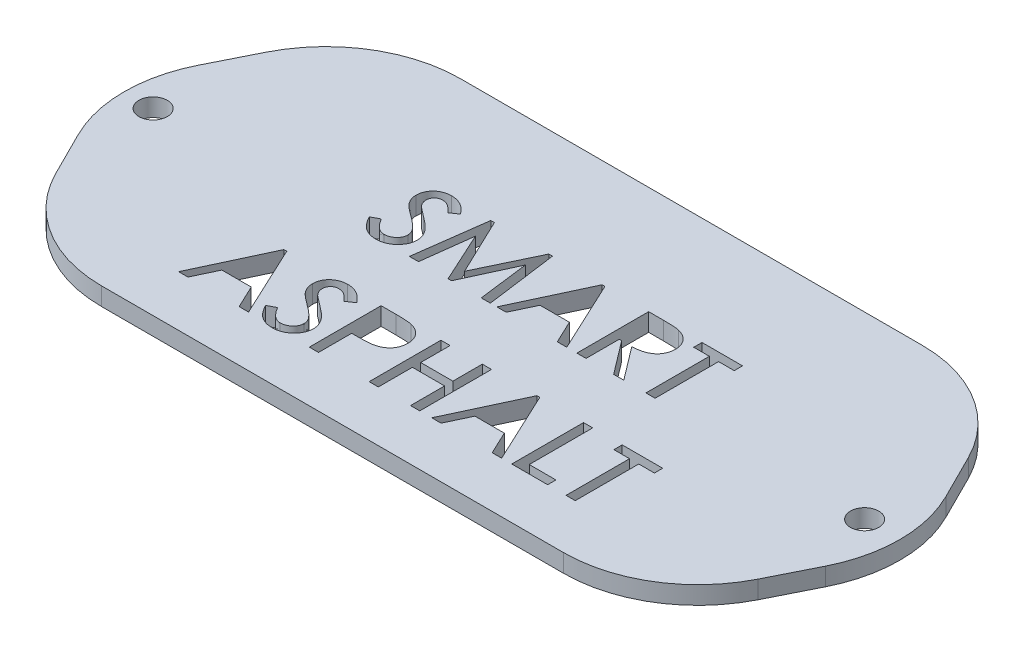
SolidWorks part; units mm, degrees
ref_plane "Front Plane" through (0, 0, 0) normal (0, 0, 1) x (1, 0, 0)
ref_plane "Top Plane" through (0, 0, 0) normal (0, 1, 0) x (1, 0, 0)
ref_plane "Right Plane" through (0, 0, 0) normal (1, 0, 0) x (0, 0, -1)
sketch "Sketch1" plane through (0, 0, 0) normal (0, 1, 0) x (1, 0, 0)
  line L0 (-31.8082, -3.672) -> (38.1918, -3.672) construction
  line L1 (-22.5377, 16.328) -> (28.9212, 16.328)
  line L2 (-31.8082, 16.328) -> (-31.8082, -23.672)
  line L3 (-22.5377, -23.672) -> (28.9212, -23.672)
  line L4 (38.1918, 16.328) -> (38.1918, -23.672)
  line L5 (-35.9541, -15.3802) -> (-38.4541, -10.3802)
  line L6 (-38.4541, 3.0362) -> (-35.9541, 8.0362)
  line L7 (42.3377, 8.0362) -> (44.8377, 3.0362)
  line L8 (44.8377, -10.3802) -> (42.3377, -15.3802)
  line L9 (-31.8082, -3.672) -> (-41.8082, -3.672) construction
  line L10 (48.1918, -3.672) -> (38.1918, -3.672) construction
  line L11 (-14.2954, -2.0854) -> (-13.4236, -1.6207)
  line L12 (-9.4749, 3.2607) -> (-10.3114, 2.687)
  line L13 (-8.2441, -3.672) -> (-7.1752, 4.328)
  line L14 (-7.1752, 4.328) -> (-6.7714, 4.328)
  line L15 (-6.7714, 4.328) -> (-3.7377, -2.0309)
  line L16 (-3.7377, -2.0309) -> (-0.7041, 4.328)
  line L17 (-0.7041, 4.328) -> (-0.2938, 4.328)
  line L18 (-0.2938, 4.328) -> (0.7815, -3.672)
  line L19 (0.7815, -3.672) -> (-0.2361, -3.672)
  line L20 (-0.2361, -3.672) -> (-0.9477, 1.9691)
  line L21 (-0.9477, 1.9691) -> (-3.5438, -3.672)
  line L22 (-3.5438, -3.672) -> (-3.9316, -3.672)
  line L23 (-3.9316, -3.672) -> (-6.5198, 1.9691)
  line L24 (-6.5198, 1.9691) -> (-7.2281, -3.672)
  line L25 (-7.2281, -3.672) -> (-8.2441, -3.672)
  line L26 (5.5507, 4.328) -> (9.2943, -3.672)
  line L27 (9.2943, -3.672) -> (8.2414, -3.672)
  line L28 (8.2414, -3.672) -> (7.0267, -1.1079)
  line L29 (7.0267, -1.1079) -> (3.7543, -1.1079)
  line L30 (3.7543, -1.1079) -> (2.5395, -3.672)
  line L31 (2.5395, -3.672) -> (1.4994, -3.672)
  line L32 (1.4994, -3.672) -> (5.2302, 4.328)
  line L33 (5.2302, 4.328) -> (5.5507, 4.328)
  line L34 (5.3905, 2.5796) -> (4.1453, -0.1848)
  line L35 (4.1453, -0.1848) -> (6.6485, -0.1848)
  line L36 (6.6485, -0.1848) -> (5.3905, 2.5796)
  line L37 (10.4225, 4.328) -> (12.0603, 4.328)
  line L38 (12.852, 0.0204) -> (15.6533, -3.672)
  line L39 (15.6533, -3.672) -> (14.5235, -3.672)
  line L40 (14.5235, -3.672) -> (11.7222, 0.0204)
  line L41 (11.7222, 0.0204) -> (11.4482, 0.0204)
  line L42 (11.4482, 0.0204) -> (11.4482, -3.672)
  line L43 (11.4482, -3.672) -> (10.4225, -3.672)
  line L44 (10.4225, -3.672) -> (10.4225, 4.328)
  line L45 (11.4482, 3.405) -> (11.4482, 0.9418)
  line L46 (11.4482, 0.9418) -> (12.6244, 0.9338)
  line L47 (12.6565, 3.405) -> (11.4482, 3.405)
  line L48 (16.3712, 3.405) -> (16.3712, 4.328)
  line L49 (16.3712, 4.328) -> (20.8841, 4.328)
  line L50 (20.8841, 4.328) -> (20.8841, 3.405)
  line L51 (20.8841, 3.405) -> (19.1405, 3.405)
  line L52 (19.1405, 3.405) -> (19.1405, -3.672)
  line L53 (19.1405, -3.672) -> (18.1148, -3.672)
  line L54 (18.1148, -3.672) -> (18.1148, 3.405)
  line L55 (18.1148, 3.405) -> (16.3712, 3.405)
  line L56 (-15.5775, -10.0053) -> (-11.8339, -18.0053)
  line L57 (-11.8339, -18.0053) -> (-12.8868, -18.0053)
  line L58 (-12.8868, -18.0053) -> (-14.1015, -15.4412)
  line L59 (-14.1015, -15.4412) -> (-17.3739, -15.4412)
  line L60 (-17.3739, -15.4412) -> (-18.5887, -18.0053)
  line L61 (-18.5887, -18.0053) -> (-19.6288, -18.0053)
  line L62 (-19.6288, -18.0053) -> (-15.898, -10.0053)
  line L63 (-15.898, -10.0053) -> (-15.5775, -10.0053)
  line L64 (-15.7377, -11.7537) -> (-16.9829, -14.5181)
  line L65 (-16.9829, -14.5181) -> (-14.4797, -14.5181)
  line L66 (-14.4797, -14.5181) -> (-15.7377, -11.7537)
  line L67 (-11.5262, -16.4187) -> (-10.6544, -15.954)
  line L68 (-6.7057, -11.0726) -> (-7.5422, -11.6463)
  line L69 (-5.0647, -10.0053) -> (-3.4252, -10.0053)
  line L70 (-3.6864, -14.313) -> (-4.039, -14.313)
  line L71 (-4.039, -14.313) -> (-4.039, -18.0053)
  line L72 (-4.039, -18.0053) -> (-5.0647, -18.0053)
  line L73 (-5.0647, -18.0053) -> (-5.0647, -10.0053)
  line L74 (-4.039, -10.9284) -> (-4.039, -13.3931)
  line L75 (-4.039, -13.3931) -> (-2.8852, -13.4059)
  line L76 (-2.8243, -10.9284) -> (-4.039, -10.9284)
  line L77 (1.602, -10.0053) -> (2.6277, -10.0053)
  line L78 (2.6277, -10.0053) -> (2.6277, -13.2873)
  line L79 (2.6277, -13.2873) -> (6.2174, -13.2873)
  line L80 (6.2174, -13.2873) -> (6.2174, -10.0053)
  line L81 (6.2174, -10.0053) -> (7.243, -10.0053)
  line L82 (7.243, -10.0053) -> (7.243, -18.0053)
  line L83 (7.243, -18.0053) -> (6.2174, -18.0053)
  line L84 (6.2174, -18.0053) -> (6.2174, -14.2104)
  line L85 (6.2174, -14.2104) -> (2.6277, -14.2104)
  line L86 (2.6277, -14.2104) -> (2.6277, -18.0053)
  line L87 (2.6277, -18.0053) -> (1.602, -18.0053)
  line L88 (1.602, -18.0053) -> (1.602, -10.0053)
  line L89 (12.6277, -10.0053) -> (16.3712, -18.0053)
  line L90 (16.3712, -18.0053) -> (15.3184, -18.0053)
  line L91 (15.3184, -18.0053) -> (14.1036, -15.4412)
  line L92 (14.1036, -15.4412) -> (10.8312, -15.4412)
  line L93 (10.8312, -15.4412) -> (9.6164, -18.0053)
  line L94 (9.6164, -18.0053) -> (8.5764, -18.0053)
  line L95 (8.5764, -18.0053) -> (12.3071, -10.0053)
  line L96 (12.3071, -10.0053) -> (12.6277, -10.0053)
  line L97 (12.4674, -11.7537) -> (11.2222, -14.5181)
  line L98 (11.2222, -14.5181) -> (13.7254, -14.5181)
  line L99 (13.7254, -14.5181) -> (12.4674, -11.7537)
  line L100 (17.4994, -10.0053) -> (18.5251, -10.0053)
  line L101 (18.5251, -10.0053) -> (18.5251, -17.0822)
  line L102 (18.5251, -17.0822) -> (21.4994, -17.0822)
  line L103 (21.4994, -17.0822) -> (21.4994, -18.0053)
  line L104 (21.4994, -18.0053) -> (17.4994, -18.0053)
  line L105 (17.4994, -18.0053) -> (17.4994, -10.0053)
  line L106 (21.8071, -10.9284) -> (21.8071, -10.0053)
  line L107 (21.8071, -10.0053) -> (26.32, -10.0053)
  line L108 (26.32, -10.0053) -> (26.32, -10.9284)
  line L109 (26.32, -10.9284) -> (24.5764, -10.9284)
  line L110 (24.5764, -10.9284) -> (24.5764, -18.0053)
  line L111 (24.5764, -18.0053) -> (23.5507, -18.0053)
  line L112 (23.5507, -18.0053) -> (23.5507, -10.9284)
  line L113 (23.5507, -10.9284) -> (21.8071, -10.9284)
  circle A0 centre (-36.8082, -3.672) radius 1.58
  circle A1 centre (42.4918, -3.672) radius 1.58
  arc A2 (28.9212, 16.328) -> (42.3377, 8.0362) centre (28.9212, 1.328) cw
  arc A3 (44.8377, 3.0362) -> (44.8377, -10.3802) centre (31.4212, -3.672) cw
  arc A4 (42.3377, -15.3802) -> (28.9212, -23.672) centre (28.9212, -8.672) cw
  arc A5 (-22.5377, -23.672) -> (-35.9541, -15.3802) centre (-22.5377, -8.672) cw
  arc A6 (-22.5377, 16.328) -> (-35.9541, 8.0362) centre (-22.5377, 1.328) ccw
  arc A7 (-38.4541, 3.0362) -> (-38.4541, -10.3802) centre (-25.0377, -3.672) ccw
  spline S0 degree 3 poles (-13.4236, -1.6207) (-13.306, -1.8238) (-13.1197, -2.1048) (-12.841, -2.429) (-12.642, -2.62) (-12.4393, -2.7675) (-12.1741, -2.9072) (-11.9597, -2.9546) (-11.8195, -2.954) knots 0 0 0 0 0.323709 0.463076 0.588607 0.70305 0.807444 1 1 1 1
  spline S1 degree 3 poles (-11.8195, -2.954) (-11.6921, -2.9547) (-11.5025, -2.9312) (-11.2598, -2.8582) (-11.0878, -2.7813) (-10.9289, -2.687) (-10.7886, -2.5748) (-10.6695, -2.4478) (-10.5714, -2.3077) (-10.4946, -2.1581) (-10.4188, -1.9518) (-10.3988, -1.7879) (-10.398, -1.68) knots 0 0 0 0 0.179726 0.268081 0.357295 0.445327 0.528558 0.610268 0.690476 0.769478 0.847321 1 1 1 1
  spline S2 degree 3 poles (-10.398, -1.68) (-10.398, -1.5542) (-10.4446, -1.2898) (-10.5783, -1.0573) (-10.6576, -0.9444) knots 0 0 0 0 0.475822 1 1 1 1
  spline S3 degree 3 poles (-10.6576, -0.9444) (-10.7288, -0.8518) (-10.8473, -0.7102) (-11.0297, -0.5268) (-11.1934, -0.3774) (-11.3748, -0.2193) (-11.6547, 0.0059) (-11.8786, 0.1728) (-12.0342, 0.2864) knots 0 0 0 0 0.189088 0.298561 0.418529 0.547897 0.688106 1 1 1 1
  spline S4 degree 3 poles (-12.0342, 0.2864) (-12.1919, 0.4) (-12.4149, 0.5655) (-12.6934, 0.7822) (-12.8676, 0.9237) (-13.0172, 1.0537) (-13.1716, 1.1982) (-13.2738, 1.3022) (-13.3275, 1.3729) knots 0 0 0 0 0.34437 0.492061 0.62526 0.741997 0.84312 1 1 1 1
  spline S5 degree 3 poles (-13.3275, 1.3729) (-13.4021, 1.4641) (-13.5002, 1.6096) (-13.6061, 1.8145) (-13.6709, 1.9692) (-13.721, 2.1269) (-13.7675, 2.3423) (-13.7847, 2.5073) (-13.7826, 2.6181) knots 0 0 0 0 0.261315 0.388035 0.511327 0.633179 0.754563 1 1 1 1
  spline S6 degree 3 poles (-13.7826, 2.6181) (-13.7832, 2.7897) (-13.7518, 3.0454) (-13.6397, 3.3665) (-13.5265, 3.5924) (-13.3818, 3.8011) (-13.2097, 3.9883) (-13.0093, 4.1502) (-12.7858, 4.2866) (-12.545, 4.3971) (-12.2048, 4.5034) (-11.9374, 4.5324) (-11.7586, 4.5332) knots 0 0 0 0 0.165741 0.24599 0.32741 0.408958 0.49035 0.572108 0.656848 0.742473 0.827298 1 1 1 1
  spline S7 degree 3 poles (-11.7586, 4.5332) (-11.5557, 4.5302) (-11.2508, 4.5037) (-10.8657, 4.3839) (-10.6347, 4.2859) (-10.4553, 4.1856) (-10.3196, 4.0951) (-10.1805, 3.9926) (-10.0424, 3.8731) (-9.9, 3.7422) (-9.7087, 3.5381) (-9.5653, 3.3773) (-9.4749, 3.2607) knots 0 0 0 0 0.224555 0.33422 0.444072 0.50082 0.560832 0.624034 0.691371 0.762286 0.837344 1 1 1 1
  spline S8 degree 3 poles (-10.3114, 2.687) (-10.3953, 2.7767) (-10.5168, 2.9057) (-10.6793, 3.0644) (-10.7899, 3.1649) (-10.8916, 3.2537) (-10.9875, 3.3277) (-11.0744, 3.3912) (-11.1831, 3.4543) (-11.3163, 3.5166) (-11.5362, 3.5922) (-11.7115, 3.6075) (-11.8275, 3.6101) knots 0 0 0 0 0.200828 0.289794 0.371424 0.445148 0.510508 0.569414 0.621107 0.715688 0.809621 1 1 1 1
  spline S9 degree 3 poles (-11.8275, 3.6101) (-11.9495, 3.6106) (-12.131, 3.5803) (-12.3492, 3.4753) (-12.4915, 3.3663) (-12.6097, 3.2312) (-12.7289, 3.0145) (-12.7557, 2.8255) (-12.757, 2.6998) knots 0 0 0 0 0.251154 0.372198 0.495422 0.617858 0.739465 1 1 1 1
  spline S10 degree 3 poles (-12.757, 2.6998) (-12.756, 2.6146) (-12.7461, 2.4862) (-12.6991, 2.3226) (-12.6547, 2.202) (-12.5925, 2.0837) (-12.4833, 1.9231) (-12.3834, 1.8104) (-12.3098, 1.7383) knots 0 0 0 0 0.234924 0.35069 0.466856 0.587688 0.716774 1 1 1 1
  spline S11 degree 3 poles (-12.3098, 1.7383) (-12.2674, 1.6959) (-12.1876, 1.6327) (-12.0696, 1.5378) (-11.9534, 1.4442) (-11.8144, 1.3412) (-11.5932, 1.1723) (-11.4139, 1.0435) (-11.289, 0.9514) knots 0 0 0 0 0.139314 0.236561 0.352442 0.486425 0.639051 1 1 1 1
  spline S12 degree 3 poles (-11.289, 0.9514) (-11.1156, 0.8256) (-10.865, 0.6409) (-10.5583, 0.3828) (-10.3549, 0.2064) (-10.177, 0.0329) (-10.0211, -0.1342) (-9.8854, -0.2932) (-9.7404, -0.4959) (-9.5956, -0.7458) (-9.4254, -1.1403) (-9.3742, -1.4528) (-9.3723, -1.6559) knots 0 0 0 0 0.191284 0.277594 0.357647 0.431479 0.499277 0.561538 0.6179 0.721501 0.818718 1 1 1 1
  spline S13 degree 3 poles (-9.3723, -1.6559) (-9.3733, -1.7973) (-9.3931, -2.0088) (-9.4664, -2.2809) (-9.5446, -2.4775) (-9.6423, -2.6691) (-9.7635, -2.8543) (-9.9077, -3.0321) (-10.0688, -3.2038) (-10.247, -3.3615) (-10.4381, -3.5004) (-10.6416, -3.6164) (-10.8557, -3.7105) (-11.0794, -3.7871) (-11.3979, -3.8585) (-11.6458, -3.8751) (-11.8131, -3.8771) knots 0 0 0 0 0.115857 0.172975 0.230355 0.288881 0.348971 0.41124 0.476257 0.54168 0.60594 0.669455 0.733135 0.797354 0.862866 1 1 1 1
  spline S14 degree 3 poles (-11.8131, -3.8771) (-11.935, -3.8755) (-12.1174, -3.8673) (-12.3549, -3.8227) (-12.5274, -3.78) (-12.6961, -3.7255) (-12.8588, -3.6559) (-13.0183, -3.5759) (-13.1736, -3.4823) (-13.3249, -3.3726) (-13.4731, -3.2453) (-13.6173, -3.0981) (-13.76, -2.933) (-13.8993, -2.748) (-14.0857, -2.4683) (-14.2132, -2.2425) (-14.2954, -2.0854) knots 0 0 0 0 0.112875 0.168078 0.223044 0.277068 0.331723 0.386485 0.441864 0.499147 0.559021 0.622216 0.689427 0.760627 0.836081 1 1 1 1
  spline S15 degree 3 poles (12.0603, 4.328) (12.2618, 4.3284) (12.5508, 4.325) (12.9184, 4.3154) (13.1544, 4.3013) (13.3646, 4.2887) (13.5921, 4.2637) (13.7496, 4.2437) (13.844, 4.2207) knots 0 0 0 0 0.337633 0.484566 0.616401 0.73399 0.837533 1 1 1 1
  spline S16 degree 3 poles (13.844, 4.2207) (13.9712, 4.1909) (14.1569, 4.1362) (14.3903, 4.0358) (14.5524, 3.9511) (14.7043, 3.855) (14.8433, 3.7448) (14.9748, 3.6261) (15.0937, 3.4951) (15.2018, 3.3558) (15.2943, 3.2083) (15.3737, 3.0545) (15.4399, 2.8946) (15.4894, 2.7268) (15.5365, 2.4916) (15.5526, 2.31) (15.5507, 2.187) knots 0 0 0 0 0.135918 0.200616 0.263977 0.325924 0.387262 0.448208 0.509937 0.570936 0.631349 0.690728 0.750765 0.811048 0.872274 1 1 1 1
  spline S17 degree 3 poles (15.5507, 2.187) (15.5514, 1.9863) (15.5149, 1.6867) (15.3788, 1.3138) (15.2645, 1.0979) (15.1531, 0.9373) (15.0599, 0.8231) (14.9573, 0.7162) (14.8463, 0.6154) (14.7238, 0.5251) (14.5936, 0.4395) (14.4541, 0.3608) (14.253, 0.2663) (13.981, 0.1678) (13.4978, 0.0513) (13.1142, 0.0232) (12.852, 0.0204) knots 0 0 0 0 0.154646 0.229433 0.304482 0.342006 0.379701 0.417797 0.455938 0.494998 0.534798 0.575853 0.618154 0.705693 0.797937 1 1 1 1
  spline S18 degree 3 poles (12.6244, 0.9338) (12.7463, 0.9333) (12.9228, 0.9365) (13.1493, 0.9516) (13.2994, 0.9677) (13.4357, 0.9869) (13.5592, 1.0084) (13.6687, 1.0374) (13.7966, 1.0792) (13.9387, 1.1464) (14.0894, 1.2487) (14.2216, 1.3697) (14.3299, 1.5115) (14.4165, 1.6671) (14.5018, 1.8906) (14.5244, 2.0703) (14.5251, 2.1902) knots 0 0 0 0 0.140831 0.203961 0.26233 0.315336 0.363053 0.407084 0.446136 0.518504 0.587865 0.656027 0.724697 0.793247 0.861253 1 1 1 1
  spline S19 degree 3 poles (14.5251, 2.1902) (14.5234, 2.3066) (14.503, 2.4828) (14.4143, 2.6994) (14.3268, 2.8513) (14.2183, 2.9878) (14.0936, 3.1082) (13.9494, 3.2036) (13.8167, 3.2679) (13.6978, 3.3083) (13.5925, 3.3332) (13.4726, 3.3553) (13.338, 3.3746) (13.1888, 3.3887) (12.9601, 3.4012) (12.781, 3.4061) (12.6565, 3.405) knots 0 0 0 0 0.138112 0.206111 0.275416 0.344634 0.411623 0.47939 0.54801 0.585345 0.627608 0.675777 0.729349 0.788339 0.852848 1 1 1 1
  spline S20 degree 3 poles (-10.6544, -15.954) (-10.5367, -16.1572) (-10.3504, -16.4382) (-10.0718, -16.7623) (-9.8727, -16.9534) (-9.6701, -17.1008) (-9.4049, -17.2406) (-9.1905, -17.2879) (-9.0502, -17.2873) knots 0 0 0 0 0.323709 0.463076 0.588607 0.70305 0.807444 1 1 1 1
  spline S21 degree 3 poles (-9.0502, -17.2873) (-8.9229, -17.288) (-8.7333, -17.2645) (-8.4906, -17.1916) (-8.3185, -17.1147) (-8.1596, -17.0203) (-8.0193, -16.9081) (-7.9003, -16.7811) (-7.8022, -16.641) (-7.7253, -16.4914) (-7.6495, -16.2851) (-7.6296, -16.1212) (-7.6288, -16.0133) knots 0 0 0 0 0.179726 0.268081 0.357295 0.445327 0.528558 0.610268 0.690476 0.769478 0.847321 1 1 1 1
  spline S22 degree 3 poles (-7.6288, -16.0133) (-7.6288, -15.8875) (-7.6754, -15.6231) (-7.8091, -15.3906) (-7.8884, -15.2777) knots 0 0 0 0 0.475822 1 1 1 1
  spline S23 degree 3 poles (-7.8884, -15.2777) (-7.9596, -15.1852) (-8.0781, -15.0435) (-8.2605, -14.8601) (-8.4242, -14.7107) (-8.6056, -14.5526) (-8.8855, -14.3274) (-9.1094, -14.1605) (-9.265, -14.047) knots 0 0 0 0 0.189088 0.298561 0.418529 0.547897 0.688106 1 1 1 1
  spline S24 degree 3 poles (-9.265, -14.047) (-9.4226, -13.9333) (-9.6457, -13.7678) (-9.9242, -13.5511) (-10.0983, -13.4096) (-10.248, -13.2797) (-10.4023, -13.1351) (-10.5045, -13.0311) (-10.5582, -12.9604) knots 0 0 0 0 0.34437 0.492061 0.62526 0.741997 0.84312 1 1 1 1
  spline S25 degree 3 poles (-10.5582, -12.9604) (-10.6329, -12.8692) (-10.731, -12.7237) (-10.8369, -12.5189) (-10.9017, -12.3641) (-10.9517, -12.2065) (-10.9983, -11.991) (-11.0155, -11.826) (-11.0134, -11.7152) knots 0 0 0 0 0.261315 0.388035 0.511327 0.633179 0.754563 1 1 1 1
  spline S26 degree 3 poles (-11.0134, -11.7152) (-11.014, -11.5436) (-10.9826, -11.2879) (-10.8704, -10.9668) (-10.7573, -10.7409) (-10.6125, -10.5323) (-10.4405, -10.345) (-10.24, -10.1831) (-10.0166, -10.0467) (-9.7758, -9.9362) (-9.4356, -9.8299) (-9.1681, -9.8009) (-8.9893, -9.8002) knots 0 0 0 0 0.165741 0.24599 0.32741 0.408958 0.49035 0.572108 0.656848 0.742473 0.827298 1 1 1 1
  spline S27 degree 3 poles (-8.9893, -9.8002) (-8.7864, -9.8031) (-8.4816, -9.8296) (-8.0964, -9.9494) (-7.8655, -10.0474) (-7.686, -10.1477) (-7.5503, -10.2383) (-7.4112, -10.3408) (-7.2732, -10.4603) (-7.1308, -10.5911) (-6.9394, -10.7953) (-6.7961, -10.956) (-6.7057, -11.0726) knots 0 0 0 0 0.224555 0.33422 0.444072 0.50082 0.560832 0.624034 0.691371 0.762286 0.837344 1 1 1 1
  spline S28 degree 3 poles (-7.5422, -11.6463) (-7.626, -11.5566) (-7.7476, -11.4276) (-7.9101, -11.2689) (-8.0206, -11.1684) (-8.1224, -11.0797) (-8.2182, -11.0057) (-8.3052, -10.9421) (-8.4138, -10.8791) (-8.547, -10.8167) (-8.7669, -10.7412) (-8.9423, -10.7258) (-9.0582, -10.7232) knots 0 0 0 0 0.200828 0.289794 0.371424 0.445148 0.510508 0.569414 0.621107 0.715688 0.809621 1 1 1 1
  spline S29 degree 3 poles (-9.0582, -10.7232) (-9.1802, -10.7228) (-9.3618, -10.753) (-9.58, -10.858) (-9.7223, -10.967) (-9.8405, -11.1022) (-9.9597, -11.3188) (-9.9865, -11.5078) (-9.9877, -11.6335) knots 0 0 0 0 0.251154 0.372198 0.495422 0.617858 0.739465 1 1 1 1
  spline S30 degree 3 poles (-9.9877, -11.6335) (-9.9868, -11.7187) (-9.9768, -11.8472) (-9.9298, -12.0107) (-9.8855, -12.1314) (-9.8233, -12.2496) (-9.7141, -12.4102) (-9.6142, -12.5229) (-9.5406, -12.595) knots 0 0 0 0 0.234924 0.35069 0.466856 0.587688 0.716774 1 1 1 1
  spline S31 degree 3 poles (-9.5406, -12.595) (-9.4981, -12.6374) (-9.4184, -12.7006) (-9.3004, -12.7956) (-9.1841, -12.8891) (-9.0452, -12.9921) (-8.824, -13.161) (-8.6447, -13.2899) (-8.5198, -13.3819) knots 0 0 0 0 0.139314 0.236561 0.352442 0.486425 0.639051 1 1 1 1
  spline S32 degree 3 poles (-8.5198, -13.3819) (-8.3463, -13.5077) (-8.0958, -13.6925) (-7.7891, -13.9505) (-7.5857, -14.1269) (-7.4078, -14.3004) (-7.2519, -14.4675) (-7.1162, -14.6265) (-6.9711, -14.8293) (-6.8264, -15.0792) (-6.6561, -15.4736) (-6.6049, -15.7861) (-6.6031, -15.9893) knots 0 0 0 0 0.191284 0.277594 0.357647 0.431479 0.499277 0.561538 0.6179 0.721501 0.818718 1 1 1 1
  spline S33 degree 3 poles (-6.6031, -15.9893) (-6.604, -16.1306) (-6.6239, -16.3421) (-6.6971, -16.6143) (-6.7754, -16.8108) (-6.8731, -17.0025) (-6.9943, -17.1876) (-7.1385, -17.3654) (-7.2996, -17.5371) (-7.4778, -17.6949) (-7.6689, -17.8337) (-7.8723, -17.9497) (-8.0865, -18.0438) (-8.3102, -18.1205) (-8.6287, -18.1918) (-8.8766, -18.2085) (-9.0438, -18.2104) knots 0 0 0 0 0.115857 0.172975 0.230355 0.288881 0.348971 0.41124 0.476257 0.54168 0.60594 0.669455 0.733135 0.797354 0.862866 1 1 1 1
  spline S34 degree 3 poles (-9.0438, -18.2104) (-9.1658, -18.2089) (-9.3482, -18.2007) (-9.5856, -18.156) (-9.7581, -18.1133) (-9.9268, -18.0589) (-10.0896, -17.9892) (-10.249, -17.9092) (-10.4043, -17.8156) (-10.5557, -17.7059) (-10.7039, -17.5786) (-10.8481, -17.4315) (-10.9908, -17.2663) (-11.1301, -17.0814) (-11.3165, -16.8016) (-11.444, -16.5758) (-11.5262, -16.4187) knots 0 0 0 0 0.112875 0.168078 0.223044 0.277068 0.331723 0.386485 0.441864 0.499147 0.559021 0.622216 0.689427 0.760627 0.836081 1 1 1 1
  spline S35 degree 3 poles (-3.4252, -10.0053) (-3.2174, -10.0034) (-2.9193, -10.0103) (-2.5405, -10.0198) (-2.2973, -10.0325) (-2.082, -10.05) (-1.8494, -10.0751) (-1.6897, -10.1012) (-1.5935, -10.1239) knots 0 0 0 0 0.339081 0.486441 0.618233 0.736286 0.838887 1 1 1 1
  spline S36 degree 3 poles (-1.5935, -10.1239) (-1.4698, -10.1523) (-1.2914, -10.2103) (-1.066, -10.3107) (-0.9088, -10.3948) (-0.7629, -10.4921) (-0.6249, -10.5977) (-0.4992, -10.7171) (-0.3814, -10.8445) (-0.2781, -10.9827) (-0.1855, -11.1272) (-0.1088, -11.2799) (-0.0457, -11.4403) (0.0036, -11.6076) (0.0518, -11.8443) (0.064, -12.0273) (0.0636, -12.1511) knots 0 0 0 0 0.133852 0.19746 0.260283 0.321746 0.382427 0.443464 0.504531 0.565317 0.625388 0.685405 0.745404 0.807138 0.869287 1 1 1 1
  spline S37 degree 3 poles (0.0636, -12.1511) (0.0639, -12.2754) (0.0519, -12.4596) (0.0036, -12.6966) (-0.0442, -12.8647) (-0.1071, -13.0248) (-0.1823, -13.1782) (-0.2731, -13.3232) (-0.3768, -13.4608) (-0.4939, -13.5888) (-0.6228, -13.7069) (-0.765, -13.8128) (-0.9192, -13.9086) (-1.0848, -13.9959) (-1.3277, -14.0982) (-1.5216, -14.154) (-1.6544, -14.1864) knots 0 0 0 0 0.128476 0.189841 0.249574 0.308808 0.367299 0.425796 0.485287 0.545053 0.604819 0.665523 0.727998 0.792177 0.858698 1 1 1 1
  spline S38 degree 3 poles (-1.6544, -14.1864) (-1.7621, -14.2121) (-1.941, -14.2404) (-2.2006, -14.2649) (-2.44, -14.2824) (-2.7088, -14.2969) (-3.1276, -14.3092) (-3.4567, -14.3141) (-3.6864, -14.313) knots 0 0 0 0 0.162726 0.266179 0.38359 0.515804 0.662049 1 1 1 1
  spline S39 degree 3 poles (-2.8852, -13.4059) (-2.7596, -13.4041) (-2.5783, -13.4022) (-2.3465, -13.386) (-2.1941, -13.3724) (-2.0555, -13.3532) (-1.9315, -13.3294) (-1.821, -13.3026) (-1.6945, -13.2605) (-1.553, -13.1947) (-1.4026, -13.0944) (-1.27, -12.9744) (-1.1605, -12.8331) (-1.0724, -12.6775) (-0.9841, -12.4541) (-0.9636, -12.2729) (-0.9621, -12.1527) knots 0 0 0 0 0.144118 0.208018 0.266518 0.31975 0.368444 0.411413 0.450186 0.521219 0.58974 0.656999 0.725552 0.793911 0.861649 1 1 1 1
  spline S40 degree 3 poles (-0.9621, -12.1527) (-0.9636, -12.0362) (-0.9847, -11.8599) (-1.0727, -11.6419) (-1.1609, -11.4885) (-1.2682, -11.3482) (-1.3953, -11.2276) (-1.5391, -11.129) (-1.6733, -11.0658) (-1.793, -11.0247) (-1.8985, -11.0006) (-2.0177, -10.978) (-2.1513, -10.9586) (-2.2995, -10.9447) (-2.5255, -10.9321) (-2.7019, -10.9272) (-2.8243, -10.9284) knots 0 0 0 0 0.13809 0.206665 0.276506 0.346708 0.414578 0.482689 0.551868 0.589197 0.632066 0.679607 0.732546 0.791526 0.855395 1 1 1 1
  dimension "D5" = 3.16
  dimension "D6" = 3.16
  dimension "D8" = 15
  dimension "D1" = 70
  dimension "D2" = 10
  dimension "D3" = 40
  dimension "D4" = 20
  dimension "D7" = 79.3
extrude "Boss-Extrude1" add sketch "Sketch1" along normal blind 2 contours L6 A7 L5 A5 L2 A6 A0 | L1 A6 L2 A5 L3 A4 L4 A2 S33 S34 L67 S20 S21 S22 S23 S24 S25 S26 S27 L68 S28 S29 S30 S31 S32 S16 S17 L38 L39 L40 L41 L42 L43 L44 L37 S15 L24 L25 L13 L14 L15 L16 L17 L18 L19 L20 L21 L22 | A4 L8 A3 L7 A2 L4 A1
